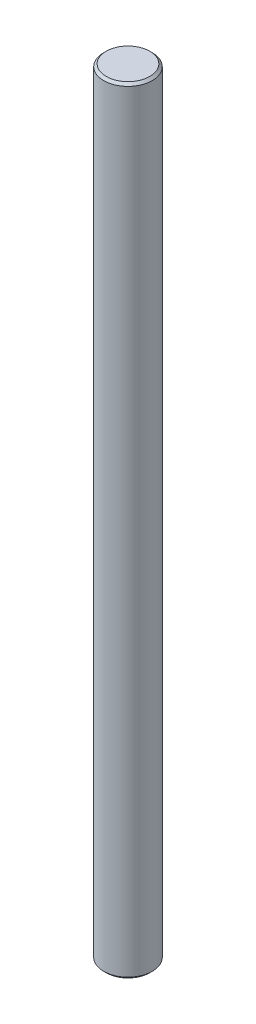
SolidWorks part; units mm, degrees
ref_plane "Front Plane" through (0, 0, 0) normal (0, 0, 1) x (1, 0, 0)
ref_plane "Top Plane" through (0, 0, 0) normal (0, 1, 0) x (1, 0, 0)
ref_plane "Right Plane" through (0, 0, 0) normal (1, 0, 0) x (0, 0, -1)
sketch "Sketch1" plane through (0, 0, 0) normal (0, 1, 0) x (1, 0, 0)
  circle A0 centre (0, 0) radius 5
  dimension "D1" = 10
extrude "Boss-Extrude1" add sketch "Sketch1" along normal blind 160
chamfer "Chamfer1" distance 0.5 angle 45 2 edges at (0, 0, 5) (0, 160, 5)
